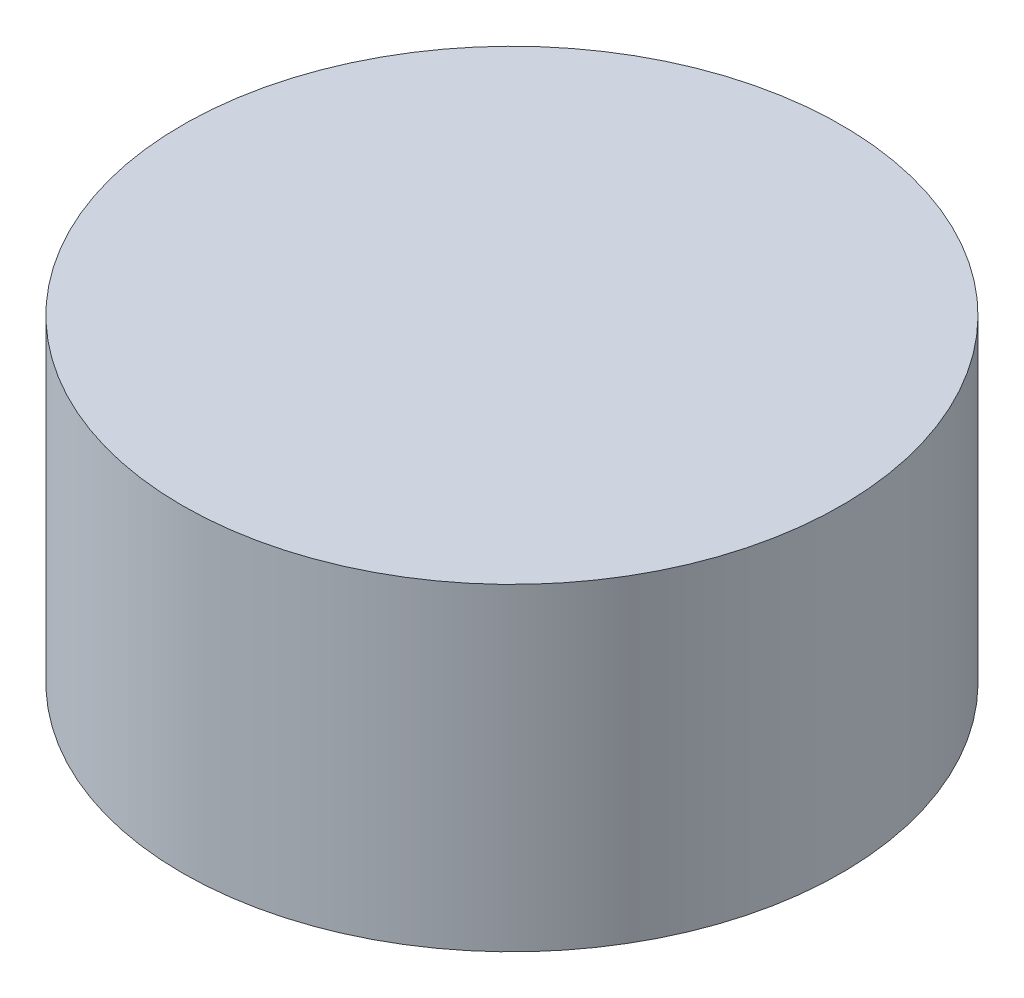
SolidWorks part; units mm, degrees
ref_plane "前视基准面" through (0, 0, 0) normal (0, 0, 1) x (1, 0, 0)
ref_plane "上视基准面" through (0, 0, 0) normal (0, 1, 0) x (1, 0, 0)
ref_plane "右视基准面" through (0, 0, 0) normal (1, 0, 0) x (0, 0, -1)
sketch "草图1" plane through (0, 0, 0) normal (0, 1, 0) x (1, 0, 0)
  circle A0 centre (0, 0) radius 29
  dimension "D1" = 58
extrude "凸台-拉伸1" add sketch "草图1" along normal blind 28
ref_plane "基准面1" through (0, 14, 0) normal (0, 1, 0) x (1, 0, 0)
